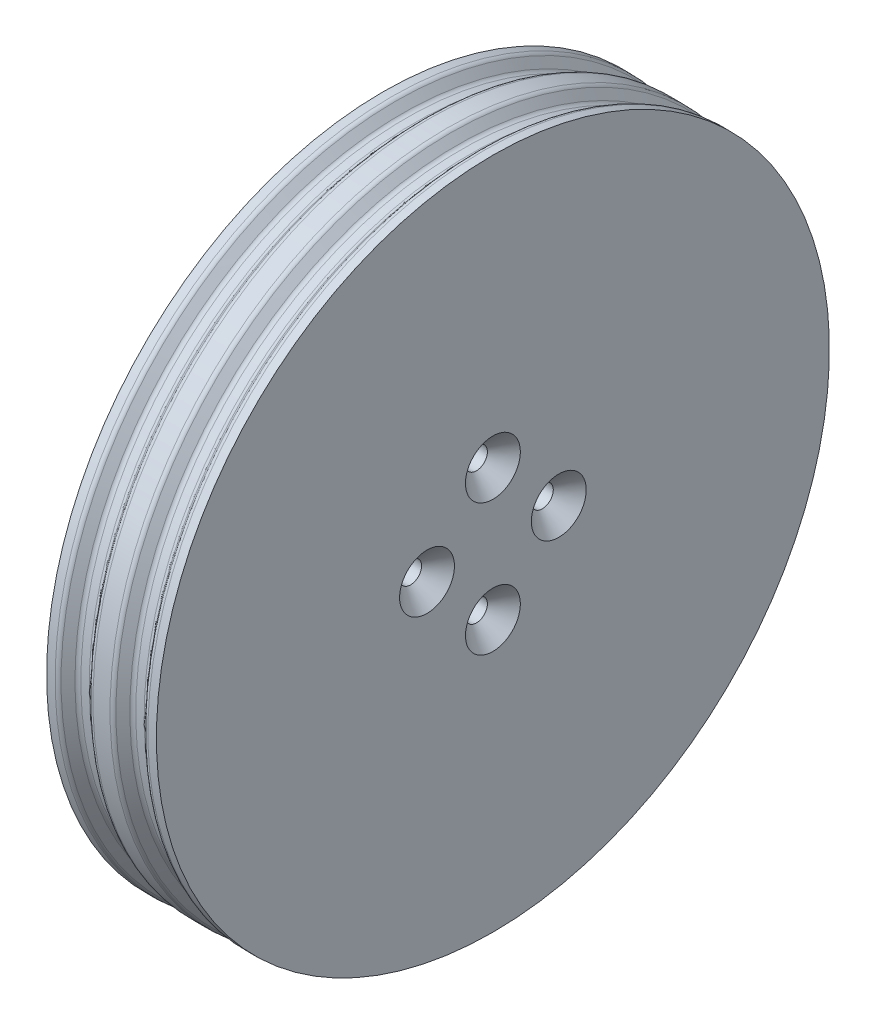
SolidWorks part; units mm, degrees
ref_plane "Piano frontale" through (0, 0, 0) normal (0, 0, 1) x (1, 0, 0)
ref_plane "Piano superiore" through (0, 0, 0) normal (0, 1, 0) x (1, 0, 0)
ref_plane "Piano destro" through (0, 0, 0) normal (1, 0, 0) x (0, 0, -1)
sketch "Schizzo1" plane through (0, 0, 0) normal (0, 0, 1) x (1, 0, 0)
  line L0 (0, 0) -> (0, 17.3)
  line L1 (0, 17.3) -> (-7, 17.3)
  line L2 (-7, 17.3) -> (-7, 30.65)
  line L6 (3, 30.65) -> (3, 0)
  line L7 (3, 0) -> (0, 0) construction
  line L9 (0, 0) -> (3, 0)
  line L10 (-5.1022, 29.65) -> (-3.8978, 29.65)
  line L11 (-3.8978, 29.65) -> (-3, 30.65)
  line L12 (-3, 30.65) -> (-1, 30.65)
  line L13 (-1, 30.65) -> (-0.1022, 29.65)
  line L14 (-0.1022, 29.65) -> (1.1022, 29.65)
  line L16 (-7, 23.975) -> (3, 23.975) construction
  line L17 (-2, 30.65) -> (-2, 23.975) construction
  line L18 (-7, 30.65) -> (-6, 30.65)
  line L19 (-6, 30.65) -> (-5.1022, 29.65)
  line L20 (1.1022, 29.65) -> (2, 30.65)
  line L21 (2, 30.65) -> (3, 30.65)
  line L22 (-4.5, 29.65) -> (-4.5, 31) construction
  circle A0 centre (-4.5, 31) radius 1.35 construction
  dimension "D4" = 2.7
  dimension "D1" = 34.6
  dimension "D2" = 3
  dimension "D3" = 10
  dimension "D5" = 1
  dimension "D6" = 2
  dimension "D7" = 1
  dimension "D8" = 31
revolve "Rivoluzione1" add sketch "Schizzo1" angle 360 about L9
sketch "Schizzo2" plane through (3, 0, 0) normal (1, 0, 0) x (0, 0, -1)
  line L0 (0, 0) -> (0, 6) construction
  circle A0 centre (0, 6) radius 1
  circle A1 centre (6, 0) radius 1
  circle A2 centre (0, -6) radius 1
  circle A3 centre (-6, 0) radius 1
  point P13 (0, 0)
  dimension "D1" = 2
  dimension "D3" = 12
  dimension "D2" = 4
extrude "Taglio-Estrusione1" cut sketch "Schizzo2" against normal blind 10
chamfer "Smusso1" distance 1.5 angle 45 4 edges at (3, 1, -6) (3, -5, 0) (3, 1, 6) (3, 7, 0)
fillet "Raccordo1" radius 0.5 8 edges at (1.1022, -29.65, 0) (-0.1022, -29.65, 0) (-3.8978, -29.65, 0) (-5.1022, -29.65, 0) (2, -30.65, 0) (-1, -30.65, 0) (-3, -30.65, 0) (-6, -30.65, 0)
